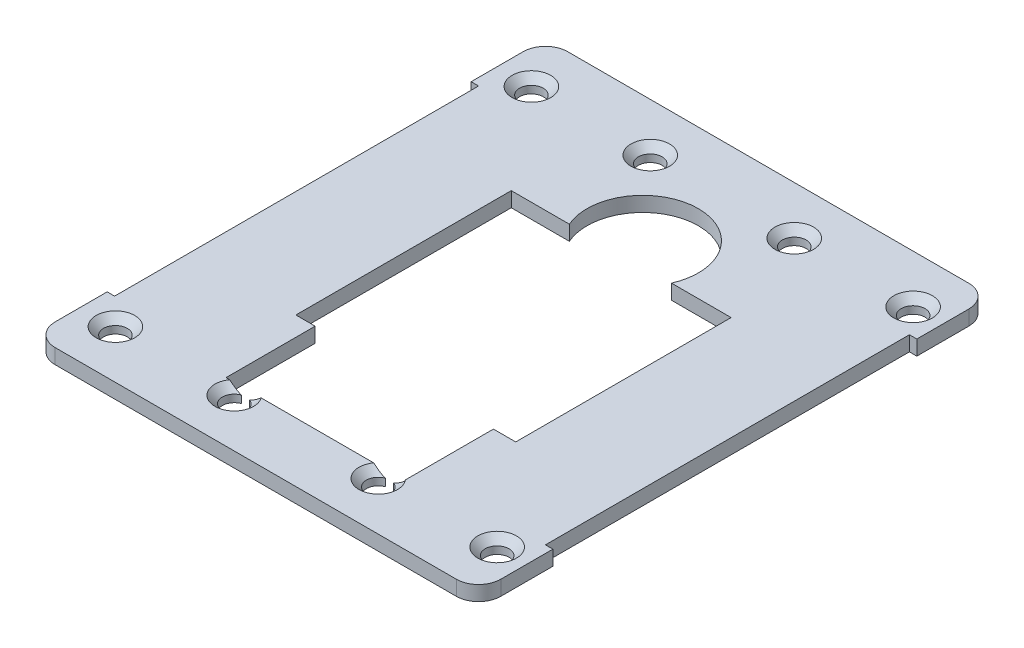
SolidWorks part; units mm, degrees
ref_plane "Front Plane" through (0, 0, 0) normal (0, 0, 1) x (1, 0, 0)
ref_plane "Top Plane" through (0, 0, 0) normal (0, 1, 0) x (1, 0, 0)
ref_plane "Right Plane" through (0, 0, 0) normal (1, 0, 0) x (0, 0, -1)
sketch "Sketch1" plane through (0, 0, 0) normal (0, 1, 0) x (1, 0, 0)
  line L0 (-12.3068, -26.3939) -> (-12.3068, -14.3939)
  line L1 (-12.3068, -14.3939) -> (-29.3068, -14.3939)
  line L2 (-29.3068, -14.3939) -> (-29.3068, -24.3939)
  line L3 (-29.3068, -24.3939) -> (-30.3068, -24.3939)
  line L4 (-30.3068, -24.3939) -> (-30.3068, -31.3939)
  line L5 (-27.3068, -34.3939) -> (-25.3068, -34.3939)
  line L6 (-25.3068, -34.3939) -> (-25.3068, -32.3939)
  line L7 (-25.3068, -32.3939) -> (-15.3068, -32.3939)
  line L8 (-15.3068, -32.3939) -> (-15.3068, -34.3939)
  line L9 (-15.3068, -34.3939) -> (12.6932, -34.3939)
  line L10 (12.6932, -34.3939) -> (12.6932, -32.3939)
  line L11 (12.6932, -32.3939) -> (22.6932, -32.3939)
  line L12 (22.6932, -32.3939) -> (22.6932, -34.3939)
  line L13 (22.6932, -34.3939) -> (26.6932, -34.3939)
  line L14 (29.6932, -31.3939) -> (29.6932, -24.3939)
  line L15 (29.6932, -24.3939) -> (28.6932, -24.3939)
  line L16 (28.6932, -24.3939) -> (28.6932, -14.3939)
  line L17 (28.6932, -14.3939) -> (11.6932, -14.3939)
  line L18 (11.6932, -14.3939) -> (11.6932, -26.3939)
  line L19 (11.6932, -26.3939) -> (-12.3068, -26.3939)
  line L20 (-30.3068, 31.6061) -> (-30.3068, 24.6061)
  line L21 (-30.3068, 24.6061) -> (-29.3068, 24.6061)
  line L22 (-29.3068, 24.6061) -> (-29.3068, 14.6061)
  line L23 (-29.3068, 14.6061) -> (28.6932, 14.6061)
  line L24 (28.6932, 14.6061) -> (28.6932, 24.6061)
  line L25 (28.6932, 24.6061) -> (29.6932, 24.6061)
  line L26 (29.6932, 24.6061) -> (29.6932, 31.6061)
  line L27 (26.6932, 34.6061) -> (24.6932, 34.6061)
  line L28 (24.6932, 34.6061) -> (24.6932, 32.6061)
  line L29 (24.6932, 32.6061) -> (14.6932, 32.6061)
  line L30 (14.6932, 32.6061) -> (14.6932, 34.6061)
  line L31 (14.6932, 34.6061) -> (-13.3068, 34.6061)
  line L32 (-13.3068, 34.6061) -> (-13.3068, 32.6061)
  line L33 (-13.3068, 32.6061) -> (-23.3068, 32.6061)
  line L34 (-23.3068, 32.6061) -> (-23.3068, 34.6061)
  line L35 (-23.3068, 34.6061) -> (-27.3068, 34.6061)
  line L36 (28.6932, 14.6061) -> (28.6932, -14.3939)
  line L37 (-29.3068, 14.6061) -> (-29.3068, -14.3939)
  line L38 (-14.9061, 14.6061) -> (-14.9061, -14.3939)
  line L39 (14.6932, -14.3939) -> (14.6932, 14.6061)
  arc A0 (-30.3068, -31.3939) -> (-27.3068, -34.3939) centre (-27.3068, -31.3939) ccw
  arc A1 (26.6932, -34.3939) -> (29.6932, -31.3939) centre (26.6932, -31.3939) ccw
  arc A2 (29.6932, 31.6061) -> (26.6932, 34.6061) centre (26.6932, 31.6061) ccw
  arc A3 (-27.3068, 34.6061) -> (-30.3068, 31.6061) centre (-27.3068, 31.6061) ccw
  circle A4 centre (-0.2122, -28.3939) radius 1.35
  circle A5 centre (19.9758, -22.3939) radius 1.35
  circle A6 centre (-20.9825, -22.3939) radius 1.35
  circle A7 centre (-0.2122, 17.6061) radius 1.35
  circle A8 centre (19.9758, 22.6061) radius 1.35
  circle A9 centre (-0.2122, 28.6061) radius 1.35
  circle A10 centre (-20.9825, 22.6061) radius 1.35
extrude "Boss-Extrude2" add sketch "Sketch1" along normal blind 2 contours L38 L23 L37 L1 | L39 L17 L36 L23 | L13 A1 L14 L15 L16 L17 L18 L19 L0 L1 L2 L3 L4 A0 L5 L6 L7 L8 L9 L10 L11 L12 A6 A5 A4 | L35 A3 L20 L21 L22 L23 L24 L25 L26 A2 L27 L28 L29 L30 L31 L32 L33 L34 A10 A9 A8 A7
sketch "Sketch2" plane through (0, 2, 0) normal (0, 1, 0) x (1, 0, 0)
  circle A0 centre (-0.2122, 17.6061) radius 7.5
  circle A1 centre (-0.2122, 17.6061) radius 1.35 construction
  dimension "D1" = 15
extrude "Cut-Extrude1" cut sketch "Sketch2" against normal blind 2
sketch "Sketch3" plane through (0, 2, 0) normal (0, 1, 0) x (1, 0, 0)
  line L1 (-23.4335, 25.6151) -> (-17.9358, 25.6151)
  line L2 (-23.4335, 25.6151) -> (-23.4335, 20.0442)
  line L3 (-23.4335, 20.0442) -> (-17.9358, 20.0442)
  line L4 (-17.9358, 25.6151) -> (-17.9358, 20.0442)
  line L5 (-4.1551, 30.3064) -> (5.0076, 30.3064)
  line L6 (-4.1551, 30.3064) -> (-4.1551, 26.4947)
  line L7 (-4.1551, 26.4947) -> (5.0076, 26.4947)
  line L8 (5.0076, 30.3064) -> (5.0076, 26.4947)
  line L9 (16.3694, 25.0287) -> (22.82, 25.0287)
  line L10 (16.3694, 25.0287) -> (16.3694, 18.8713)
  line L11 (16.3694, 18.8713) -> (22.82, 18.8713)
  line L12 (22.82, 25.0287) -> (22.82, 18.8713)
  line L13 (17.249, -19.3922) -> (22.82, -19.3922)
  line L14 (17.249, -19.3922) -> (17.249, -23.9369)
  line L15 (17.249, -23.9369) -> (22.82, -23.9369)
  line L16 (22.82, -19.3922) -> (22.82, -23.9369)
  line L17 (-4.1551, -26.7553) -> (2.1231, -26.7553)
  line L18 (-4.1551, -26.7553) -> (-4.1551, -30.4116)
  line L19 (-4.1551, -30.4116) -> (2.1231, -30.4116)
  line L20 (2.1231, -26.7553) -> (2.1231, -30.4116)
  line L21 (-23.4335, -20.2771) -> (-17.0955, -20.2771)
  line L22 (-23.4335, -20.2771) -> (-23.4335, -24.4512)
  line L23 (-23.4335, -24.4512) -> (-17.0955, -24.4512)
  line L24 (-17.0955, -20.2771) -> (-17.0955, -24.4512)
extrude "Boss-Extrude3" add sketch "Sketch3" against normal up to vertex (2 mm away)
sketch "Sketch4" plane through (0, 2, 0) normal (0, 1, 0) x (1, 0, 0)
  line L0 (14.6932, 34.6061) -> (-13.3068, 34.6061) construction
  line L1 (29.6932, 24.6061) -> (29.6932, 31.6061) construction
  line L2 (0, 37.8629) -> (0, -39.3278)
  line L3 (-51.0868, 0.1061) -> (48.659, 0.1061)
  line L4 (-15.3068, -34.3939) -> (12.6932, -34.3939) construction
  circle A0 centre (9.6932, 28.1061) radius 1.6
  circle A1 centre (25.6932, 28.1061) radius 1.6
  circle A2 centre (-25.6932, 28.1061) radius 1.6
  circle A3 centre (-9.6932, 28.1061) radius 1.6
  circle A4 centre (25.6932, -27.8939) radius 1.6
  circle A5 centre (9.6932, -27.8939) radius 1.6
  circle A6 centre (-9.6932, -27.8939) radius 1.6
  circle A7 centre (-25.6932, -27.8939) radius 1.6
  line M13 (11.6932, -26.3939) -> (-12.3068, -26.3939)
  dimension "D1" = 6.5
  dimension "D2" = 6.5
  dimension "D3" = 4
  dimension "D4" = 20
  dimension "D5" = 3.2
  dimension "D6" = 3.2
  dimension "D7" = 34.5
extrude "Cut-Extrude2" cut sketch "Sketch4" against normal blind 10 contours A6 M13 | A7 | A5 M13 | A4 | A1 | A0 | A3 | A2
chamfer "Chamfer1" distance 1 angle 45 8 edges at (-25.6932, 2, -26.5061) (-9.6932, 2, -26.5061) (9.6932, 2, -26.5061) (25.6932, 2, -26.5061) (25.6932, 2, 29.4939) (9.6932, 2, 29.4939) (-25.6932, 2, 29.4939) (-9.6932, 2, 29.4939)
sketch "Sketch5" plane through (0, 2, 0) normal (0, 1, 0) x (1, 0, 0)
  line L1 (14.6932, 34.6061) -> (25.5065, 34.6061)
  line L2 (14.6932, 34.6061) -> (14.6932, 32.3357)
  line L3 (14.6932, 32.3357) -> (25.5065, 32.3357)
  line L4 (25.5065, 34.6061) -> (25.5065, 32.3357)
  line L5 (-23.3068, 34.6061) -> (-12.9199, 34.6061)
  line L6 (-23.3068, 34.6061) -> (-23.3068, 32.0227)
  line L7 (-23.3068, 32.0227) -> (-12.9199, 32.0227)
  line L8 (-12.9199, 34.6061) -> (-12.9199, 32.0227)
  line L9 (-26.1913, -31.7711) -> (-15.3068, -31.7711)
  line L10 (-26.1913, -31.7711) -> (-26.1913, -34.3939)
  line L11 (-26.1913, -34.3939) -> (-15.3068, -34.3939)
  line L12 (-15.3068, -31.7711) -> (-15.3068, -34.3939)
  line L13 (10.6416, -31.0712) -> (22.6932, -31.0712)
  line L14 (10.6416, -31.0712) -> (10.6416, -34.3939)
  line L15 (10.6416, -34.3939) -> (22.6932, -34.3939)
  line L16 (22.6932, -31.0712) -> (22.6932, -34.3939)
extrude "Boss-Extrude4" add sketch "Sketch5" against normal up to vertex (2 mm away)
